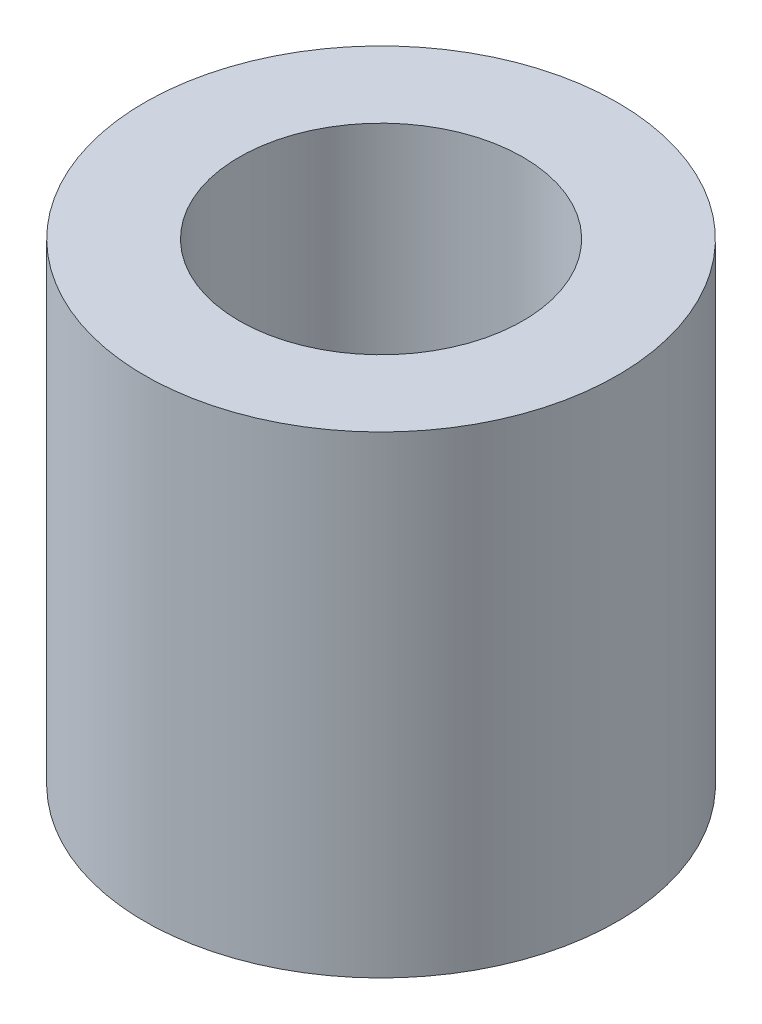
SolidWorks part; units mm, degrees
ref_plane "Front Plane" through (0, 0, 0) normal (0, 0, 1) x (1, 0, 0)
ref_plane "Top Plane" through (0, 0, 0) normal (0, 1, 0) x (1, 0, 0)
ref_plane "Right Plane" through (0, 0, 0) normal (1, 0, 0) x (0, 0, -1)
sketch "Sketch1" plane through (0, 0, 0) normal (0, 0, 1) x (1, 0, 0)
  line L0 (0, 0) -> (0, 3.3466) construction
  line L1 (1.5, 0) -> (2.5, 0)
  line L2 (1.5, 0) -> (1.5, 5)
  line L3 (1.5, 5) -> (2.5, 5)
  line L4 (2.5, 0) -> (2.5, 5)
  line L5 (1.5, 0) -> (2.5, 5) construction
  line L6 (1.5, 5) -> (2.5, 0) construction
  point P4 (2, 2.5)
  dimension "D1" = 1
  dimension "D2" = 1.5
  dimension "D3" = 5
revolve "Revolve1" add sketch "Sketch1" angle 360 about L0
